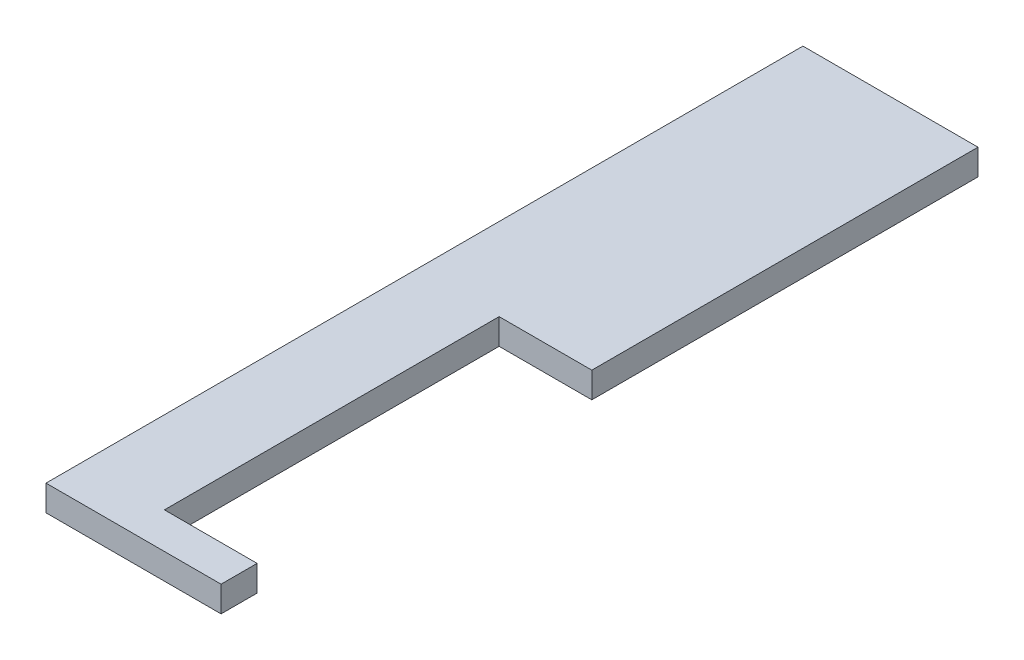
SolidWorks part; units mm, degrees
ref_plane "Front Plane" through (0, 0, 0) normal (0, 0, 1) x (1, 0, 0)
ref_plane "Top Plane" through (0, 0, 0) normal (0, 1, 0) x (1, 0, 0)
ref_plane "Right Plane" through (0, 0, 0) normal (1, 0, 0) x (0, 0, -1)
sketch "Sketch1" plane through (0, 0, 0) normal (0, 1, 0) x (1, 0, 0)
  line L0 (0, 0) -> (0, -147)
  line L1 (0, -147) -> (34, -147)
  line L2 (34, -147) -> (34, -140)
  line L3 (34, -140) -> (16, -140)
  line L4 (16, -140) -> (16, -75)
  line L5 (16, -75) -> (34, -75)
  line L7 (34, 0) -> (0, 0)
  line L9 (34, 0) -> (34, -75)
  dimension "D1" = 147
  dimension "D2" = 34
  dimension "D3" = 18
  dimension "D4" = 65
  dimension "D5" = 75
extrude "Boss-Extrude1" add sketch "Sketch1" along normal blind 5
